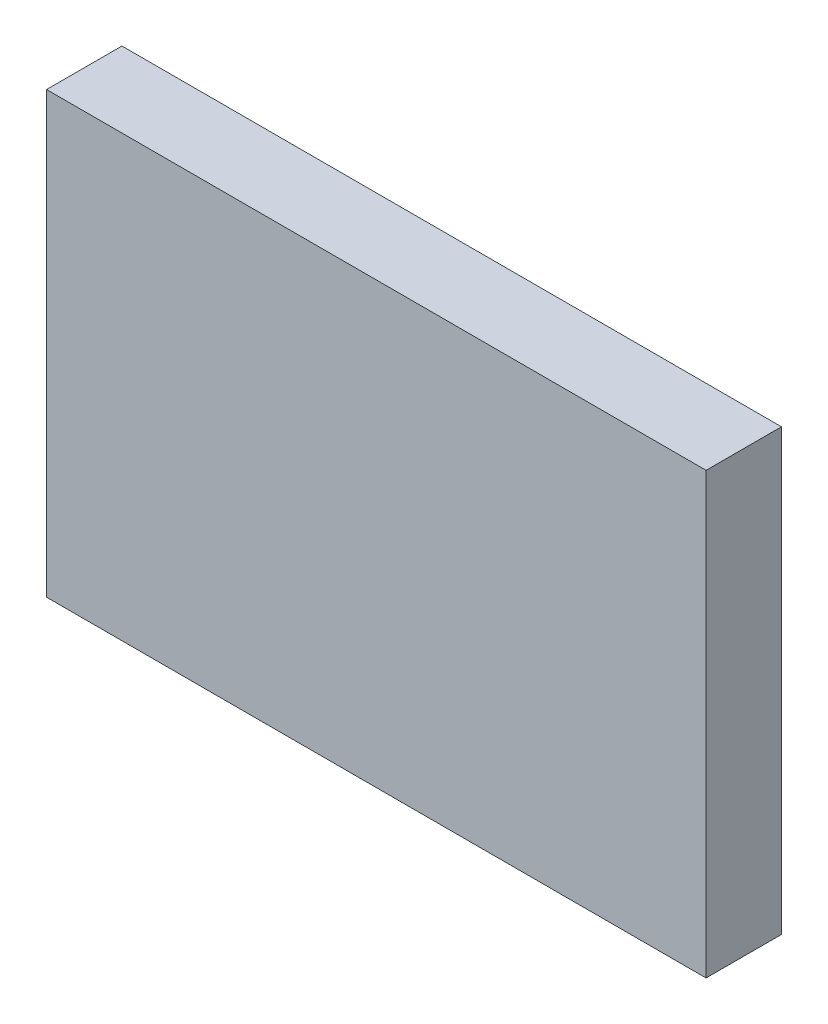
SolidWorks part; units mm, degrees
ref_plane "Front Plane" through (0, 0, 0) normal (0, 0, 1) x (1, 0, 0)
ref_plane "Top Plane" through (0, 0, 0) normal (0, 1, 0) x (1, 0, 0)
ref_plane "Right Plane" through (0, 0, 0) normal (1, 0, 0) x (0, 0, -1)
sketch "Sketch1" plane through (0, 0, 0) normal (0, 0, 1) x (1, 0, 0)
  line L1 (0, 0) -> (84, 0)
  line L2 (0, 0) -> (0, 56)
  line L3 (0, 56) -> (84, 56)
  line L4 (84, 0) -> (84, 56)
  dimension "D1" = 84
  dimension "D2" = 56
extrude "Boss-Extrude1" add sketch "Sketch1" along normal blind 9.6
